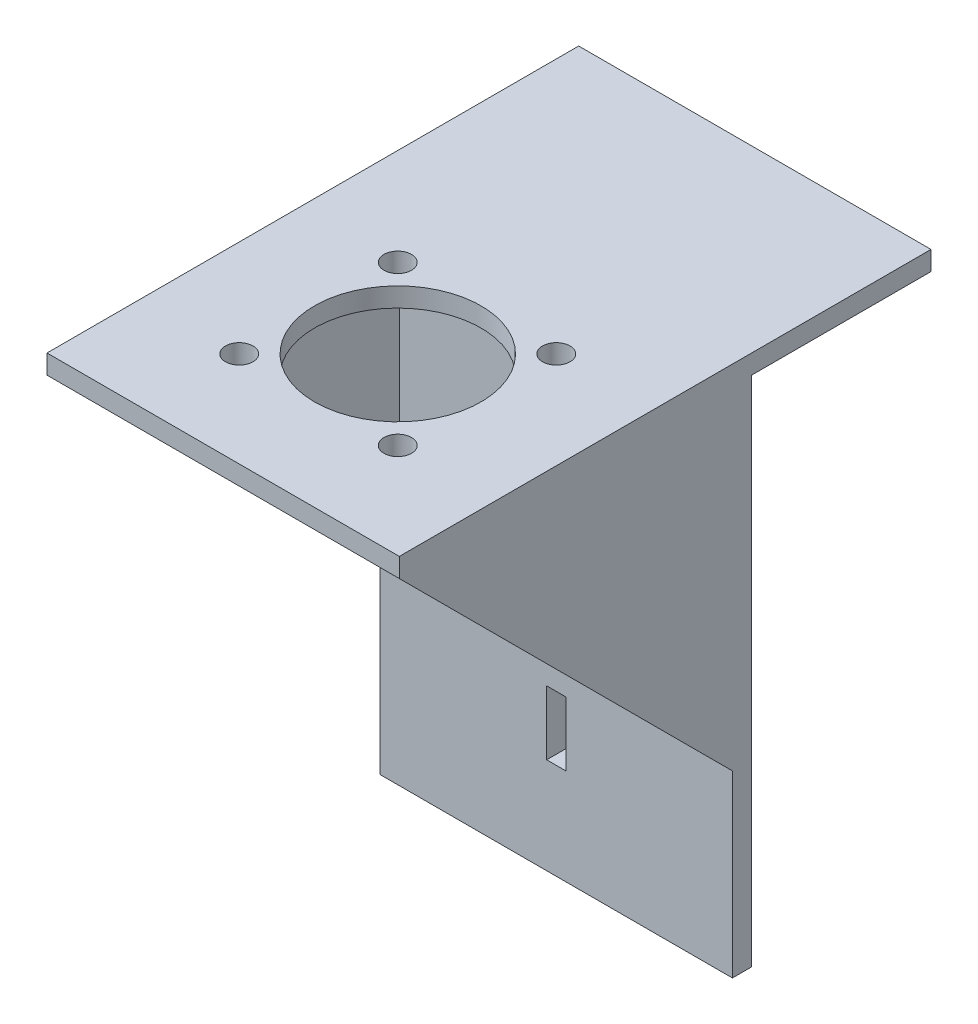
SolidWorks part; units mm, degrees
ref_plane "Front Plane" through (0, 0, 0) normal (0, 0, 1) x (1, 0, 0)
ref_plane "Top Plane" through (0, 0, 0) normal (0, 1, 0) x (1, 0, 0)
ref_plane "Right Plane" through (0, 0, 0) normal (1, 0, 0) x (0, 0, -1)
sketch "Sketch1" plane through (0, 0, 0) normal (0, 1, 0) x (1, 0, 0)
  line L0 (-27.5, 15) -> (27.5, 15) construction
  line L1 (-27.5, 40) -> (27.5, 40)
  line L2 (-27.5, 40) -> (-27.5, -40)
  line L3 (-27.5, -40) -> (27.5, -40)
  line L4 (27.5, 40) -> (27.5, -40)
  line L5 (0, -12.7439) -> (0, 4.7561) construction
  line L6 (0, 4.7561) -> (17.5, -12.7439) construction
  line L7 (17.5, -12.7439) -> (0, -12.7439) construction
  line L8 (0, -12.7439) -> (12.3744, -0.3696) construction
  circle A0 centre (0, -12.7439) radius 13
  circle A1 centre (0, -12.7439) radius 17.5 construction
  circle A2 centre (12.3744, -0.3696) radius 2.15
  circle A3 centre (12.3744, -25.1183) radius 2.15
  circle A4 centre (-12.3744, -25.1183) radius 2.15
  circle A5 centre (-12.3744, -0.3696) radius 2.15
  point P24 (0, -12.7439)
  dimension "D4" = 26
  dimension "D6" = 35
  dimension "D7" = 4.3
  dimension "D1" = 55
  dimension "D2" = 80
  dimension "D3" = 25
  dimension "D9" = 10.2439
  dimension "D5" = 4.5
  dimension "D8" = 4
extrude "Boss-Extrude2" add sketch "Sketch1" along normal blind 3
sketch "Sketch2" plane through (0, 0, 0) normal (0, -1, 0) x (1, 0, 0)
  line L0 (-27.5, -15) -> (27.5, -15) construction
  line L1 (-27.5, -40) -> (-27.5, 40) construction
  line L2 (27.5, 40) -> (27.5, -40) construction
  line L3 (27.5, -40) -> (-27.5, -40) construction
  line L4 (27.5, 40) -> (27.5, -40) construction
  line L5 (-27.5, -15) -> (27.5, -15)
  line L6 (-27.5, -15) -> (-27.5, -12)
  line L7 (-27.5, -12) -> (27.5, -12)
  line L8 (27.5, -15) -> (27.5, -12)
  dimension "D1" = 25
  dimension "D2" = 3
  dimension "D3" = 55
extrude "Boss-Extrude3" add sketch "Sketch2" along normal blind 80
sketch "Sketch3" plane through (0, 0, -15) normal (0, 0, -1) x (-1, 0, 0)
  line L0 (27.5, -60) -> (-27.5, -60) construction
  line L1 (27.5, -80) -> (27.5, 0) construction
  line L2 (-27.5, -80) -> (-27.5, 0) construction
  line L3 (27.5, 0) -> (-27.5, 0) construction
  line L4 (0, -60) -> (0, 0) construction
  line L5 (0, 0) -> (0, -80) construction
  line L6 (27.5, -80) -> (-27.5, -80) construction
  line L7 (-1.5, -55) -> (1.5, -65) construction
  line L8 (-1.5, -55) -> (1.5, -55)
  line L9 (-1.5, -55) -> (-1.5, -65)
  line L10 (-1.5, -65) -> (1.5, -65)
  line L11 (1.5, -55) -> (1.5, -65)
  dimension "D1" = 60
  dimension "D2" = 10
  dimension "D3" = 3
extrude "Cut-Extrude1" cut sketch "Sketch3" against normal blind 80
sketch "Sketch4" plane through (0, 0, -40) normal (0, 0, -1) x (-1, 0, 0)
  line L1 (-27.5, 3) -> (27.5, 3)
  line L2 (-27.5, 3) -> (-27.5, -22)
  line L3 (-27.5, -22) -> (27.5, -22)
  line L4 (27.5, 3) -> (27.5, -22)
  dimension "D1" = 55
  dimension "D2" = 25
extrude "Boss-Extrude4" add sketch "Sketch4" along normal blind 3
sketch "Sketch5" plane through (0, -22, 0) normal (0, -1, 0) x (1, 0, 0)
  line L1 (27.5, -43) -> (-27.5, -43)
  line L2 (27.5, -43) -> (27.5, -40)
  line L3 (27.5, -40) -> (-27.5, -40)
  line L4 (-27.5, -43) -> (-27.5, -40)
extrude "Cut-Extrude2" cut sketch "Sketch5" against normal blind 22
sketch "Sketch6" plane through (27.5, 0, 0) normal (1, 0, 0) x (0, 0, -1)
  line L0 (-40, 0) -> (12, 0)
  line L1 (12, 0) -> (12, -52)
  line L2 (12, -80) -> (12, 0) construction
  line L3 (12, -52) -> (-40, 0)
extrude "Boss-Extrude5" add sketch "Sketch6" against normal blind 3
sketch "Sketch7" plane through (-27.5, 0, 0) normal (-1, 0, 0) x (0, 0, 1)
  line L0 (-12, 0) -> (40, 0)
  line L1 (40, 0) -> (-12, -52)
  line L3 (-12, -52) -> (-12, 0)
extrude "Boss-Extrude6" add sketch "Sketch7" against normal blind 3
